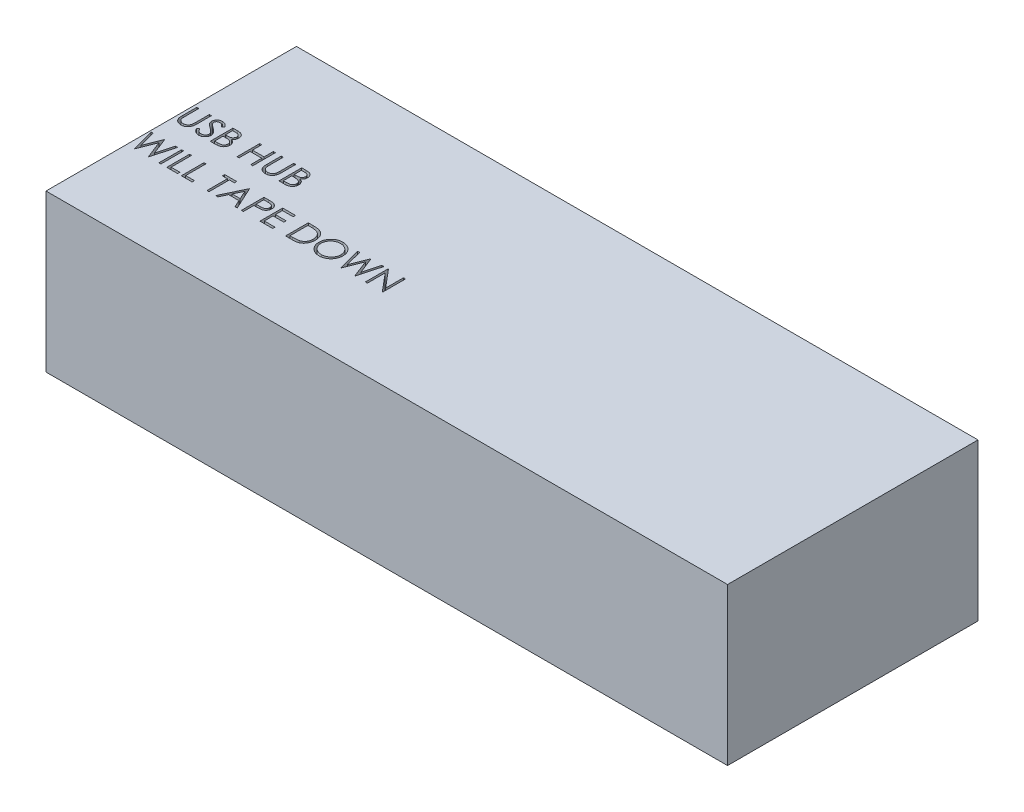
SolidWorks part; units mm, degrees
ref_plane "Front Plane" through (0, 0, 0) normal (0, 0, 1) x (1, 0, 0)
ref_plane "Top Plane" through (0, 0, 0) normal (0, 1, 0) x (1, 0, 0)
ref_plane "Right Plane" through (0, 0, 0) normal (1, 0, 0) x (0, 0, -1)
sketch "Sketch1" plane through (0, 0, 0) normal (0, 1, 0) x (1, 0, 0)
  line L1 (0, 0) -> (105.04, 0)
  line L2 (0, 0) -> (0, 38.6)
  line L3 (0, 38.6) -> (105.04, 38.6)
  line L4 (105.04, 0) -> (105.04, 38.6)
  dimension "D1" = 105.04
  dimension "D2" = 38.6
extrude "Boss-Extrude1" add sketch "Sketch1" along normal blind 24.17
sketch "Sketch2" plane through (0, 24.17, 0) normal (0, 1, 0) x (1, 0, 0)
  line L0 (0, 19.3) -> (105.04, 19.3) construction
  line L1 (0, 38.6) -> (0, 0) construction
  line L2 (105.04, 0) -> (105.04, 38.6) construction
  text T0 "USB HUB\r\nWILL TAPE DOWN"
extrude "Cut-Extrude1" cut sketch "Sketch2" against normal through all
